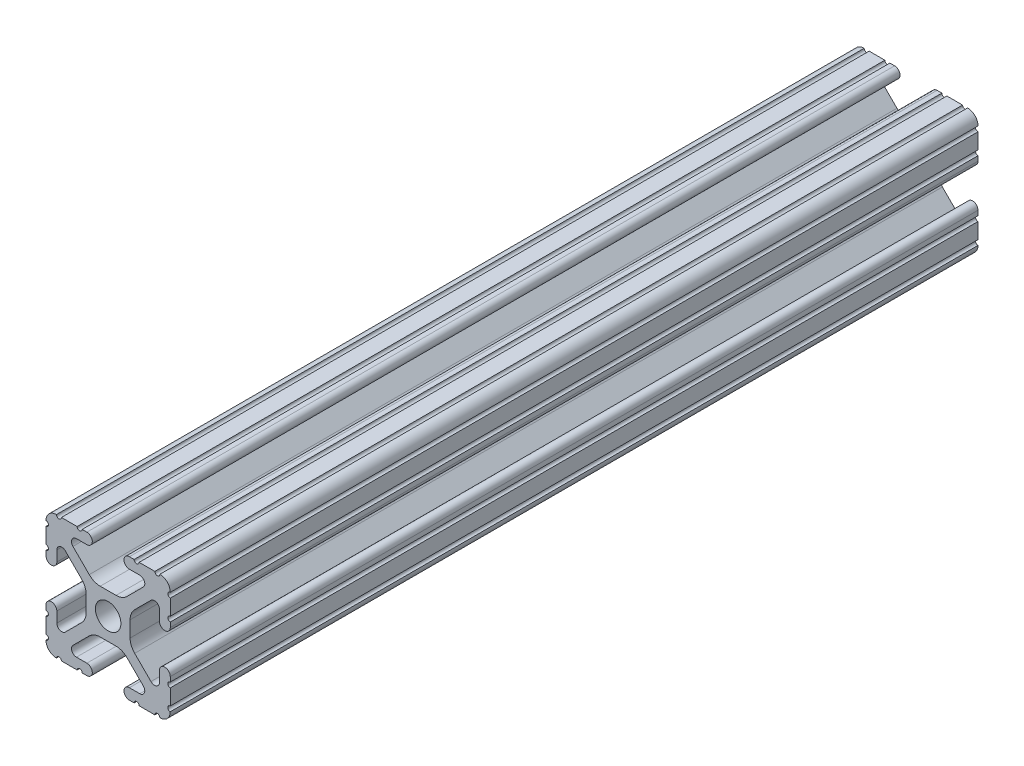
SolidWorks part; units mm, degrees
material "6061-T6 (SS)"
ref_plane "Front Plane" through (0, 0, 0) normal (0, 0, 1) x (1, 0, 0)
ref_plane "Top Plane" through (0, 0, 0) normal (0, 1, 0) x (1, 0, 0)
ref_plane "Right Plane" through (0, 0, 0) normal (1, 0, 0) x (0, 0, -1)
ref_plane "Plane1" through (0, 0, -450.85) normal (0, 0, -1) x (-1, 0, 0)
sketch "Sketch1" plane through (0, 0, -450.85) normal (0, 0, -1) x (-1, 0, 0)
  line L0 (12.7, -9.5504) -> (12.7, -6.3331)
  line L1 (12.7, -5.3171) -> (12.7, -4.3434)
  line L2 (10.4902, -4.3434) -> (10.4902, -6.4748)
  line L3 (8.7558, -7.1932) -> (5.4257, -3.8632)
  line L4 (4.4958, -1.6181) -> (4.4958, 1.6181)
  line L5 (5.4257, 3.8632) -> (8.7558, 7.1932)
  line L6 (10.4902, 6.4748) -> (10.4902, 4.3434)
  line L7 (12.7, 4.3434) -> (12.7, 5.3171)
  line L8 (12.7, 6.3331) -> (12.7, 9.5504)
  line L9 (9.5504, 12.7) -> (6.3331, 12.7)
  line L10 (5.3171, 12.7) -> (4.3434, 12.7)
  line L11 (4.3434, 10.4902) -> (6.4748, 10.4902)
  line L12 (7.1932, 8.7558) -> (3.8632, 5.4257)
  line L13 (1.6181, 4.4958) -> (-1.6181, 4.4958)
  line L14 (-3.8632, 5.4257) -> (-7.1932, 8.7558)
  line L15 (-6.4748, 10.4902) -> (-4.3434, 10.4902)
  line L16 (-4.3434, 12.7) -> (-5.3171, 12.7)
  line L17 (-6.3331, 12.7) -> (-9.5504, 12.7)
  line L18 (-12.7, 9.5504) -> (-12.7, 6.3331)
  line L19 (-12.7, 5.3171) -> (-12.7, 4.3434)
  line L20 (-10.4902, 4.3434) -> (-10.4902, 6.4748)
  line L21 (-8.7558, 7.1932) -> (-5.4257, 3.8632)
  line L22 (-4.4958, 1.6181) -> (-4.4958, -1.6181)
  line L23 (-5.4257, -3.8632) -> (-8.7558, -7.1932)
  line L24 (-10.4902, -6.4748) -> (-10.4902, -4.3434)
  line L25 (-12.7, -4.3434) -> (-12.7, -5.3171)
  line L26 (-12.7, -6.3331) -> (-12.7, -9.5504)
  line L27 (-9.5504, -12.7) -> (-6.3331, -12.7)
  line L28 (-5.3171, -12.7) -> (-4.3434, -12.7)
  line L29 (-4.3434, -10.4902) -> (-6.4748, -10.4902)
  line L30 (-7.1932, -8.7558) -> (-3.8632, -5.4257)
  line L31 (-1.6181, -4.4958) -> (1.6181, -4.4958)
  line L32 (3.8632, -5.4257) -> (7.1932, -8.7558)
  line L33 (6.4748, -10.4902) -> (4.3434, -10.4902)
  line L34 (4.3434, -12.7) -> (5.3171, -12.7)
  line L35 (6.3331, -12.7) -> (9.5504, -12.7)
  arc A0 (12.6998, -10.5664) -> (12.7, -9.5504) centre (12.7, -10.0584) cw
  arc A1 (12.7, -6.3331) -> (12.7, -5.3171) centre (12.7, -5.8251) cw
  arc A2 (12.7, -4.3434) -> (10.4902, -4.3434) centre (11.5951, -4.3434) ccw
  arc A3 (10.4902, -6.4748) -> (8.7558, -7.1932) centre (9.4742, -6.4748) cw
  arc A4 (5.4257, -3.8632) -> (4.4958, -1.6181) centre (7.6708, -1.6181) cw
  arc A5 (4.4958, 1.6181) -> (5.4257, 3.8632) centre (7.6708, 1.6181) cw
  arc A6 (8.7558, 7.1932) -> (10.4902, 6.4748) centre (9.4742, 6.4748) cw
  arc A7 (10.4902, 4.3434) -> (12.7, 4.3434) centre (11.5951, 4.3434) ccw
  arc A8 (12.7, 5.3171) -> (12.7, 6.3331) centre (12.7, 5.8251) cw
  arc A9 (12.7, 9.5504) -> (12.6998, 10.5664) centre (12.7, 10.0584) cw
  arc A10 (12.6998, 10.5664) -> (10.5664, 12.6998) centre (10.5918, 10.5918) ccw
  arc A11 (10.5664, 12.6998) -> (9.5504, 12.7) centre (10.0584, 12.7) cw
  arc A12 (6.3331, 12.7) -> (5.3171, 12.7) centre (5.8251, 12.7) cw
  arc A13 (4.3434, 12.7) -> (4.3434, 10.4902) centre (4.3434, 11.5951) ccw
  arc A14 (6.4748, 10.4902) -> (7.1932, 8.7558) centre (6.4748, 9.4742) cw
  arc A15 (3.8632, 5.4257) -> (1.6181, 4.4958) centre (1.6181, 7.6708) cw
  arc A16 (-1.6181, 4.4958) -> (-3.8632, 5.4257) centre (-1.6181, 7.6708) cw
  arc A17 (-7.1932, 8.7558) -> (-6.4748, 10.4902) centre (-6.4748, 9.4742) cw
  arc A18 (-4.3434, 10.4902) -> (-4.3434, 12.7) centre (-4.3434, 11.5951) ccw
  arc A19 (-5.3171, 12.7) -> (-6.3331, 12.7) centre (-5.8251, 12.7) cw
  arc A20 (-9.5504, 12.7) -> (-10.5664, 12.6998) centre (-10.0584, 12.7) cw
  arc A21 (-10.5664, 12.6998) -> (-12.6998, 10.5664) centre (-10.5918, 10.5918) ccw
  arc A22 (-12.6998, 10.5664) -> (-12.7, 9.5504) centre (-12.7, 10.0584) cw
  arc A23 (-12.7, 6.3331) -> (-12.7, 5.3171) centre (-12.7, 5.8251) cw
  arc A24 (-12.7, 4.3434) -> (-10.4902, 4.3434) centre (-11.5951, 4.3434) ccw
  arc A25 (-10.4902, 6.4748) -> (-8.7558, 7.1932) centre (-9.4742, 6.4748) cw
  arc A26 (-5.4257, 3.8632) -> (-4.4958, 1.6181) centre (-7.6708, 1.6181) cw
  arc A27 (-4.4958, -1.6181) -> (-5.4257, -3.8632) centre (-7.6708, -1.6181) cw
  arc A28 (-8.7558, -7.1932) -> (-10.4902, -6.4748) centre (-9.4742, -6.4748) cw
  arc A29 (-10.4902, -4.3434) -> (-12.7, -4.3434) centre (-11.5951, -4.3434) ccw
  arc A30 (-12.7, -5.3171) -> (-12.7, -6.3331) centre (-12.7, -5.8251) cw
  arc A31 (-12.7, -9.5504) -> (-12.6998, -10.5664) centre (-12.7, -10.0584) cw
  arc A32 (-12.6998, -10.5664) -> (-10.5664, -12.6998) centre (-10.5918, -10.5918) ccw
  arc A33 (-10.5664, -12.6998) -> (-9.5504, -12.7) centre (-10.0584, -12.7) cw
  arc A34 (-6.3331, -12.7) -> (-5.3171, -12.7) centre (-5.8251, -12.7) cw
  arc A35 (-4.3434, -12.7) -> (-4.3434, -10.4902) centre (-4.3434, -11.5951) ccw
  arc A36 (-6.4748, -10.4902) -> (-7.1932, -8.7558) centre (-6.4748, -9.4742) cw
  arc A37 (-3.8632, -5.4257) -> (-1.6181, -4.4958) centre (-1.6181, -7.6708) cw
  arc A38 (1.6181, -4.4958) -> (3.8632, -5.4257) centre (1.6181, -7.6708) cw
  arc A39 (7.1932, -8.7558) -> (6.4748, -10.4902) centre (6.4748, -9.4742) cw
  arc A40 (4.3434, -10.4902) -> (4.3434, -12.7) centre (4.3434, -11.5951) ccw
  arc A41 (5.3171, -12.7) -> (6.3331, -12.7) centre (5.8251, -12.7) cw
  arc A42 (9.5504, -12.7) -> (10.5664, -12.6998) centre (10.0584, -12.7) cw
  arc A43 (10.5664, -12.6998) -> (12.6998, -10.5664) centre (10.5918, -10.5918) ccw
  circle A44 centre (0, 0) radius 2.6035
extrude "Boss-Extrude1" add sketch "Sketch1" against normal mid plane 165.1
sketch "Sketch2" plane through (0, 0, 0) normal (1, 0, 0) x (0, 0, -1)
  line L0 (368.3, -12.6998) -> (533.4, -12.6998) construction
  line L1 (358.7496, -34.6212) -> (542.9504, -34.6212)
  line L2 (358.7496, -34.6212) -> (358.7496, 34.6212)
  line L3 (358.7496, 34.6212) -> (542.9504, 34.6212)
  line L4 (542.9504, -34.6212) -> (542.9504, 34.6212)
  line L5 (358.7496, -34.6212) -> (542.9504, 34.6212) construction
  line L6 (358.7496, 34.6212) -> (542.9504, -34.6212) construction
  point P0 (450.85, 0)
  point P8 (450.85, -12.6998)
  dimension "D1" = 184.2008
